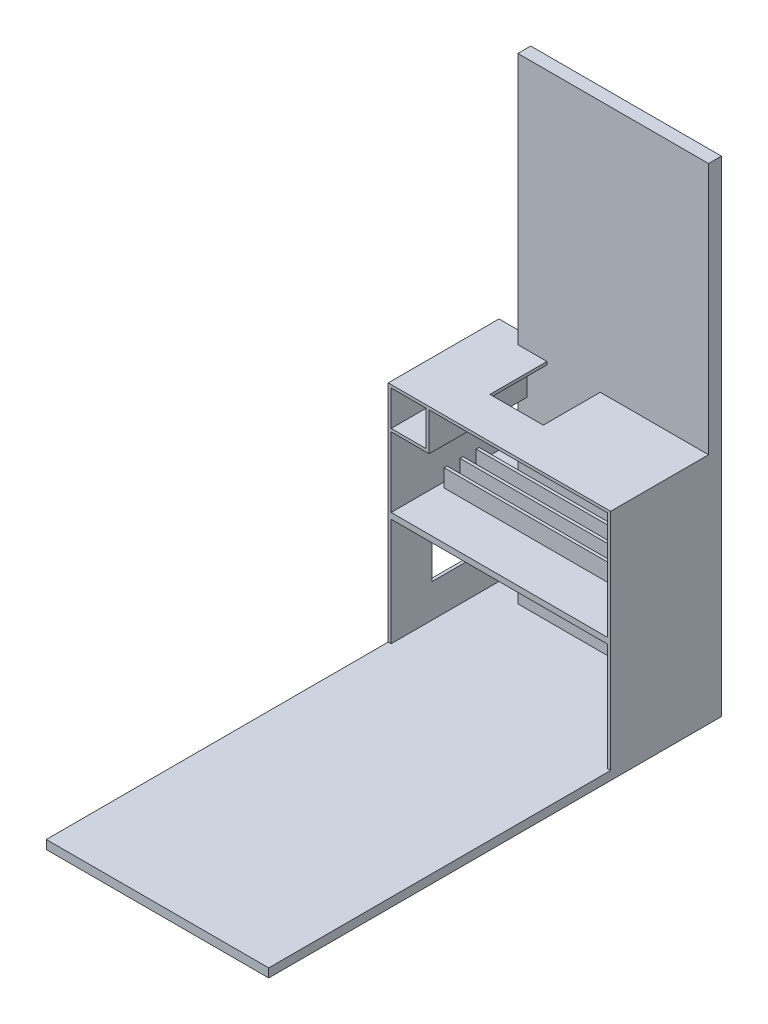
SolidWorks part; units mm, degrees
ref_plane "Front Plane" through (0, 0, 0) normal (0, 0, 1) x (1, 0, 0)
ref_plane "Top Plane" through (0, 0, 0) normal (0, 1, 0) x (1, 0, 0)
ref_plane "Right Plane" through (0, 0, 0) normal (1, 0, 0) x (0, 0, -1)
ref_plane "Plane1" through (0, 0, 38431.7002) normal (0, 0, -1) x (-1, 0, 0)
sketch "Sketch1" plane through (0, 0, 38431.7002) normal (0, 0, -1) x (-1, 0, 0)
  line L0 (14521.6177, 19917.4814) -> (14521.6177, -20082.5186)
  line L1 (7996.6177, 19917.4814) -> (42361.227, 19917.4814)
  line L2 (7996.6177, 19917.4814) -> (7996.6177, -23832.5186)
  line L3 (7996.6177, -23832.5186) -> (42361.227, -23832.5186)
  line L4 (42361.227, 19917.4814) -> (42361.227, -23832.5186)
  line L5 (14521.6177, -20082.5186) -> (42361.227, -20082.5186)
  line L6 (42361.227, -20082.5186) -> (37444.5603, 19917.4814)
  line L7 (37444.5603, 19917.4814) -> (14521.6177, 19917.4814)
  line L8 (14521.6177, 3507.4814) -> (7996.6177, 3507.4814)
  line L9 (14521.6177, 19917.4814) -> (14521.6177, 3507.4814)
  dimension "D1" = 11550
  dimension "D2" = 3750
  dimension "D3" = 27340
extrude "Boss-Extrude1" add sketch "Sketch1" against normal up to surface (440 mm away) contours L8 L0 L1 L2
sketch "Sketch2" plane through (0, 0, 38431.7002) normal (0, 0, -1) x (-1, 0, 0)
  line L0 (7996.6177, 3507.4814) -> (7996.6177, 19917.4814) construction
  line L5 (8096.6177, 3607.4814) -> (8096.6177, 3507.4814) construction
  line L10 (7996.6177, 11287.4814) -> (15606.6177, 11287.4814)
  line L11 (7996.6177, 11287.4814) -> (7996.6177, 7397.4814)
  line L16 (7996.6177, 7397.4814) -> (15606.6177, 7397.4814)
  line L17 (15606.6177, 11287.4814) -> (15606.6177, 7397.4814)
  line L18 (15606.6177, 7397.4814) -> (7996.6177, 7397.4814)
  line L23 (15606.6177, 7397.4814) -> (15606.6177, 3507.4814)
  line L32 (15606.6177, 3507.4814) -> (7996.6177, 3507.4814)
  line L33 (7996.6177, 7397.4814) -> (7996.6177, 3507.4814)
  line L34 (7996.6177, 19917.4814) -> (19527.2909, 19917.4814)
  line L39 (7996.6177, 19917.4814) -> (7996.6177, 3507.4814) construction
  line L40 (19527.2909, 19917.4814) -> (19527.2909, 14843.3368)
  line L41 (7996.6177, 11287.4814) -> (7996.6177, 19917.4814)
  line L43 (19527.2909, 14843.3368) -> (19427.2909, 14843.3368)
  line L44 (19427.2909, 14843.3368) -> (19427.2909, 19817.4814)
  line L49 (19427.2909, 19817.4814) -> (8096.6177, 19817.4814)
  line L50 (8096.6177, 19817.4814) -> (8096.6177, 11287.4814)
  line L51 (14521.6177, 19917.4814) -> (7996.6177, 19917.4814) construction
  line L52 (8096.6177, 19817.4814) -> (8096.6177, 19917.4814) construction
  line L53 (8096.6177, 19817.4814) -> (7996.6177, 19817.4814) construction
  line L54 (19427.2909, 19817.4814) -> (19527.2909, 19817.4814) construction
  line L55 (15506.6177, 7497.4814) -> (8096.6177, 7497.4814)
  line L56 (15506.6177, 7497.4814) -> (15506.6177, 11187.4814)
  line L58 (8096.6177, 7497.4814) -> (8096.6177, 11187.4814)
  line L59 (15506.6177, 3607.4814) -> (8096.6177, 3607.4814)
  line L60 (15506.6177, 3607.4814) -> (15506.6177, 7297.4814)
  line L61 (15506.6177, 7297.4814) -> (8096.6177, 7297.4814)
  line L62 (8096.6177, 3607.4814) -> (8096.6177, 7297.4814)
  line L63 (7996.6177, 3607.4814) -> (8096.6177, 3607.4814) construction
  line L64 (7996.6177, 7497.4814) -> (8096.6177, 7497.4814) construction
  line L65 (8096.6177, 7397.4814) -> (8096.6177, 7497.4814) construction
  line L66 (15506.6177, 7397.4814) -> (15506.6177, 7297.4814) construction
  line L67 (15506.6177, 7297.4814) -> (15606.6177, 7297.4814) construction
  line L68 (15506.6177, 11187.4814) -> (6942.0533, 11187.4814)
  line L69 (15506.6177, 11187.4814) -> (15506.6177, 11287.4814) construction
  line L71 (14306.6177, 9987.4814) -> (14206.6177, 9987.4814) construction
  line L72 (15606.6177, 11287.4814) -> (14052.2578, 11287.4814)
  line L73 (15606.6177, 11287.4814) -> (15606.6177, 9901.3422)
  line L74 (15506.6177, 9887.4814) -> (14206.6177, 9887.4814)
  line L75 (14206.6177, 11187.4814) -> (14206.6177, 9887.4814)
  line L76 (15606.6177, 11287.4814) -> (14152.2578, 11287.4814)
  line L77 (15606.6177, 11287.4814) -> (15606.6177, 10001.3422)
  line L78 (15506.6177, 9987.4814) -> (14306.6177, 9987.4814)
  line L79 (14306.6177, 11187.4814) -> (14306.6177, 9987.4814)
  line L80 (14306.6177, 9987.4814) -> (14306.6177, 9887.4814) construction
  dimension "D1" = 100
  dimension "D2" = 100
  dimension "D3" = 3890
  dimension "D4" = 7610
  dimension "D5" = 100
  dimension "D6" = 1200
ref_plane "Plane2" through (0, 0, 40421.7002) normal (0, 0, 1) x (1, 0, 0)
extrude "Boss-Extrude2" add sketch "Sketch2" against normal blind 3790
sketch "Sketch3" plane through (0, 11287.4814, 0) normal (0, 1, 0) x (1, 0, 0)
  line L0 (-7996.6177, -38871.7002) -> (-14521.6177, -38871.7002) construction
  line L1 (-11701.6533, -40821.7002) -> (-13525.6533, -40821.7002)
  line L2 (-11701.6533, -40821.7002) -> (-11701.6533, -38871.7002)
  line L3 (-11701.6533, -38871.7002) -> (-13525.6533, -38871.7002)
  line L4 (-13525.6533, -40821.7002) -> (-13525.6533, -38871.7002)
  point P4 (-13525.6533, -38871.7002)
  dimension "D1" = 1950
  dimension "D2" = 1824
extrude "Cut-Extrude1" cut sketch "Sketch3" against normal blind 665 from surface at 0 starting at face at (-12708.2843, 11287.4814, 39841.7002)
sketch "Sketch4" plane through (-15606.6177, 0, 0) normal (-1, 0, 0) x (0, 0, 1)
  line L0 (38871.7002, 14917.4814) -> (38871.7002, 14667.4814) construction
  line L1 (40821.7002, 11015.577) -> (38871.7002, 11015.577)
  line L2 (40821.7002, 11015.577) -> (40821.7002, 10165.577)
  line L3 (40821.7002, 10165.577) -> (38871.7002, 10165.577)
  line L4 (38871.7002, 11015.577) -> (38871.7002, 10165.577)
  line L5 (40821.7002, 6309.5798) -> (38871.7002, 6309.5798)
  line L6 (40821.7002, 6309.5798) -> (40821.7002, 4751.9117)
  line L7 (40821.7002, 4751.9117) -> (38871.7002, 4751.9117)
  line L8 (38871.7002, 6309.5798) -> (38871.7002, 4751.9117)
  dimension "D1" = 1950
  dimension "D2" = 850
extrude "Cut-Extrude2" cut sketch "Sketch4" against normal blind 736 contours L6 L5 L8 L7 | L2 L1 L4 L3
sketch "Sketch5" plane through (0, 7497.4814, 0) normal (0, 1, 0) x (1, 0, 0)
  line L0 (-8270.8001, -40589.2413) -> (-8096.6177, -40589.2413) construction
  line L1 (-8270.8001, -40589.2413) -> (-15332.4353, -40589.2413)
  line L2 (-8270.8001, -40589.2413) -> (-8270.8001, -40489.2413)
  line L3 (-8270.8001, -40489.2413) -> (-15332.4353, -40489.2413)
  line L4 (-15332.4353, -40589.2413) -> (-15332.4353, -40489.2413)
  line L5 (-8096.6177, -42221.7002) -> (-8096.6177, -38871.7002) construction
  line L6 (-15332.4353, -40589.2413) -> (-15506.6177, -40589.2413) construction
  line L7 (-15506.6177, -42221.7002) -> (-15506.6177, -38431.7002) construction
  dimension "D1" = 100
extrude "Boss-Extrude3" add sketch "Sketch5" along normal blind 600
pattern_linear "LPattern1" count 3 spacing 550 along (0, 0, -1) of "Boss-Extrude3"
sketch "Sketch7" plane through (0, 0, 38421.7002) normal (0, 0, -1) x (-1, 0, 0)
  line L0 (14521.6177, 3607.4814) -> (8096.6177, 3607.4814) construction
  line L1 (7996.6177, 3307.4814) -> (15606.6177, 3307.4814)
  line L2 (7996.6177, 3307.4814) -> (7996.6177, 3607.4814)
  line L3 (7996.6177, 3607.4814) -> (15606.6177, 3607.4814)
  line L4 (15606.6177, 3307.4814) -> (15606.6177, 3607.4814)
  line L6 (7996.6177, 19917.4814) -> (7996.6177, 3507.4814) construction
  line L7 (15606.6177, 11287.4814) -> (15606.6177, 3507.4814) construction
  dimension "D1" = 300
extrude "Boss-Extrude4" add sketch "Sketch7" against normal blind 15500
